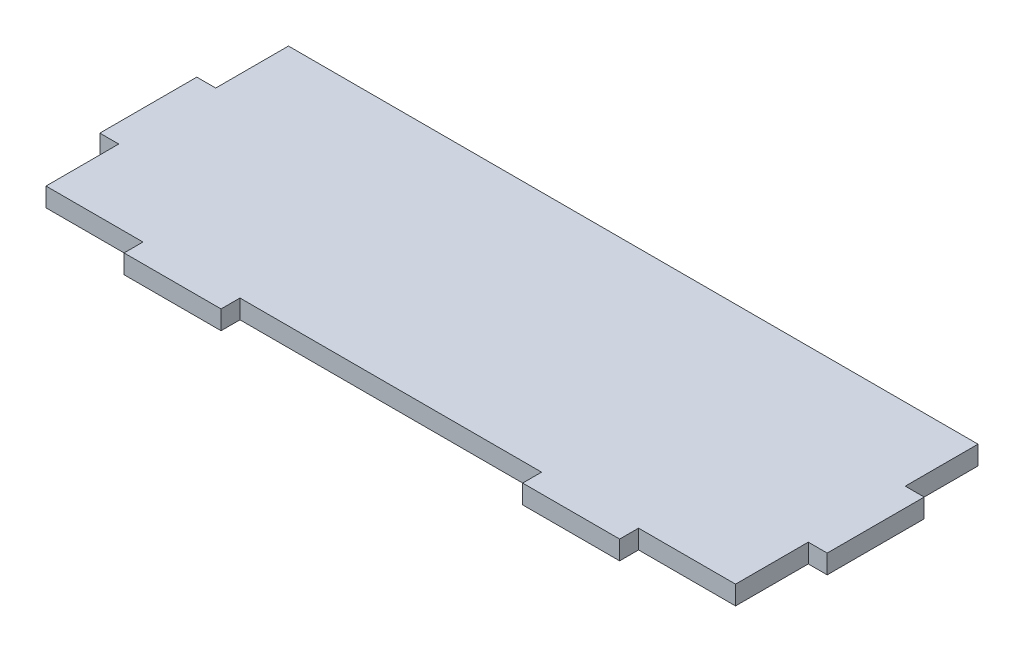
SolidWorks part; units mm, degrees
material "Very Low Density PE (SS)"
ref_plane "Front Plane" through (0, 0, 0) normal (0, 0, 1) x (1, 0, 0)
ref_plane "Top Plane" through (0, 0, 0) normal (0, 1, 0) x (1, 0, 0)
ref_plane "Right Plane" through (0, 0, 0) normal (1, 0, 0) x (0, 0, -1)
sketch "Sketch1" plane through (0, 0, 0) normal (0, 1, 0) x (1, 0, 0)
  line L2 (-71.1, 25) -> (-71.1, 10)
  line L5 (0, -21.1) -> (0, 25) construction
  line L6 (-75, 0) -> (75, 0) construction
  line L24 (71.1, 25) -> (71.1, 10)
  line L42 (-71.1, -25) -> (-51.1, -25)
  line L65 (71.1, 10) -> (75, 10)
  line L66 (75, 10) -> (75, -10)
  line L67 (75, -10) -> (71.1, -10)
  line L68 (71.1, -10) -> (71.1, -25)
  line L69 (-71.1, 10) -> (-75, 10)
  line L70 (-71.1, 25) -> (71.1, 25)
  line L71 (-75, 10) -> (-75, -10)
  line L72 (-71.1, -10) -> (-71.1, -25)
  line L73 (-75, -10) -> (-71.1, -10)
  line L74 (-51.1, -25) -> (-51.1, -28.9)
  line L75 (-51.1, -28.9) -> (-31.1, -28.9)
  line L76 (-31.1, -28.9) -> (-31.1, -25)
  line L77 (-31.1, -25) -> (31.1, -25)
  line L78 (31.1, -25) -> (31.1, -28.9)
  line L79 (31.1, -28.9) -> (51.1, -28.9)
  line L80 (51.1, -28.9) -> (51.1, -25)
  line L81 (51.1, -25) -> (71.1, -25)
  point P0 (0, 0)
  dimension "D2" = 50
  dimension "D3" = 20
  dimension "D4" = 20
  dimension "D5" = 20
  dimension "D6" = 25
  dimension "D7" = 20
  dimension "D8" = 3.9
  dimension "D9" = 150
  dimension "D10" = 3.9
  dimension "D11" = 20
  dimension "D12" = 3.9
extrude "Boss-Extrude1" add sketch "Sketch1" along normal blind 3.9
